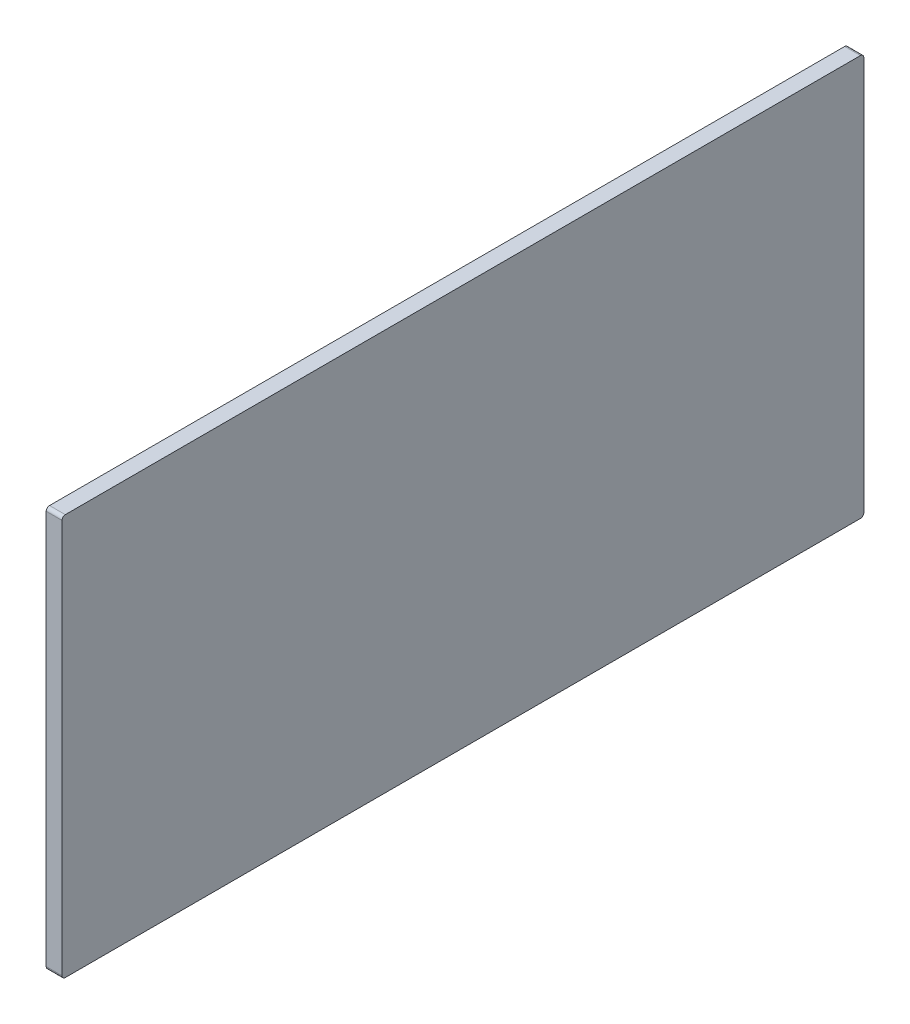
SolidWorks part; units mm, degrees
material "Delrin 2700 NC010, Low Viscosity Acetal Copolymer (SS)"
ref_plane "Front Plane" through (0, 0, 0) normal (0, 0, 1) x (1, 0, 0)
ref_plane "Top Plane" through (0, 0, 0) normal (0, 1, 0) x (1, 0, 0)
ref_plane "Right Plane" through (0, 0, 0) normal (1, 0, 0) x (0, 0, -1)
sketch "Sketch1" plane through (-311.15, 0, 0) normal (-1, 0, 0) x (0, 0, 1)
  line L0 (273.05, 463.55) -> (-273.05, 463.55) construction
  line L1 (-304.8, 482.6) -> (304.8, 482.6)
  line L2 (-304.8, 482.6) -> (-304.8, 177.8)
  line L3 (-304.8, 177.8) -> (304.8, 177.8)
  line L4 (304.8, 482.6) -> (304.8, 177.8)
  line L5 (-285.75, 450.85) -> (-285.75, 209.55) construction
  point P6 (0, 463.55)
  point P7 (0, 482.6)
  point P10 (-285.75, 330.2)
  point P11 (-304.8, 330.2)
  dimension "D1" = 609.6
  dimension "D2" = 304.8
extrude "Boss-Extrude1" add sketch "Sketch1" along normal blind 11.9888
fillet "Fillet1" radius 2.54 4 edges at (-317.1444, 482.6, -304.8) (-317.1444, 177.8, -304.8) (-317.1444, 177.8, 304.8) (-317.1444, 482.6, 304.8)
